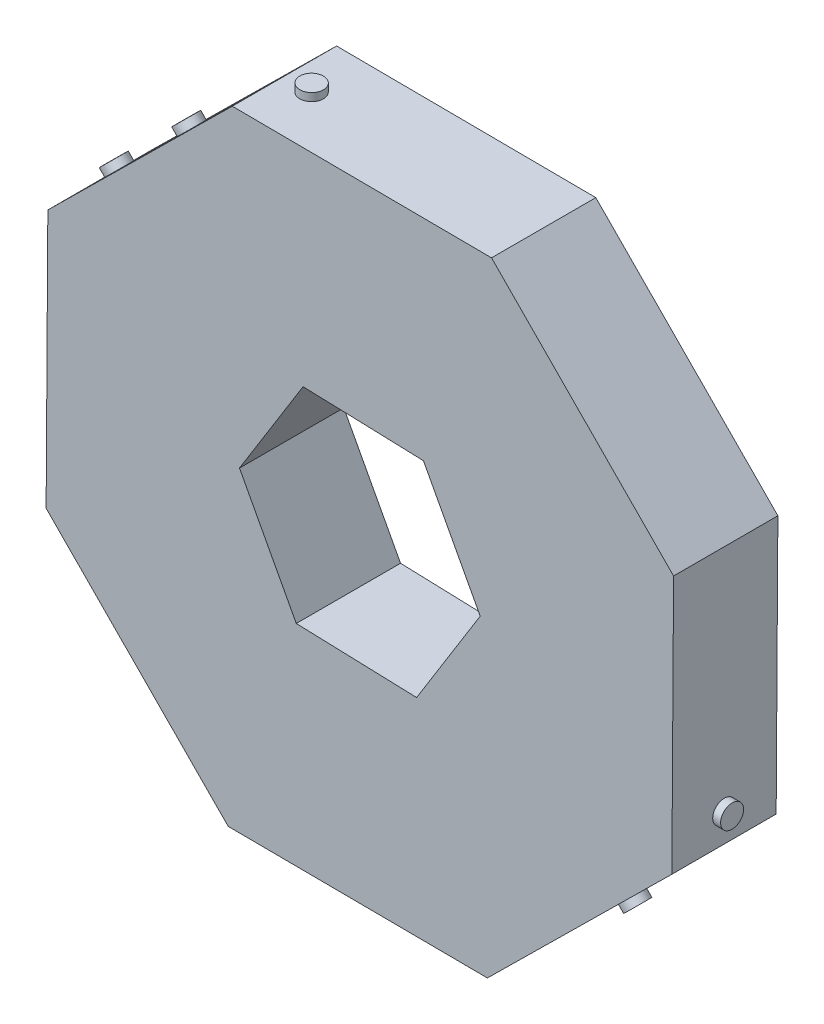
SolidWorks part; units mm, degrees
ref_plane "Front Plane" through (0, 0, 0) normal (0, 0, 1) x (1, 0, 0)
ref_plane "Top Plane" through (0, 0, 0) normal (0, 1, 0) x (1, 0, 0)
ref_plane "Right Plane" through (0, 0, 0) normal (1, 0, 0) x (0, 0, -1)
sketch "Sketch1" plane through (0, 0, 0) normal (0, 0, 1) x (1, 0, 0)
  line L1 (-7.7649, 19.1017) -> (-18.9975, 8.0163)
  line L2 (-18.9975, 8.0163) -> (-19.1017, -7.7649)
  line L3 (-19.1017, -7.7649) -> (-8.0163, -18.9975)
  line L4 (-8.0163, -18.9975) -> (7.7649, -19.1017)
  line L5 (7.7649, -19.1017) -> (18.9975, -8.0163)
  line L6 (18.9975, -8.0163) -> (19.1017, 7.7649)
  line L7 (19.1017, 7.7649) -> (8.0163, 18.9975)
  line L8 (8.0163, 18.9975) -> (-7.7649, 19.1017)
  circle A0 centre (0, 0) radius 19.05 construction
  dimension "D1" = 38.1
extrude "Boss-Extrude1" add sketch "Sketch1" along normal blind 6.35
sketch "Sketch2" plane through (0.1257, 19.0496, 0) normal (0.0066, 1, 0) x (1, -0.0066, 0)
  line L0 (-7.8908, -6.35) -> (-7.8908, 0) construction
  line L1 (7.8908, 0) -> (-7.8908, 0) construction
  circle A0 centre (-6.2398, -3.175) radius 0.72
  dimension "D1" = 1.44
  dimension "D2" = 1.651
  dimension "D3" = 3.175
extrude "Boss-Extrude2" add sketch "Sketch2" along normal blind 0.48
sketch "Sketch3" plane through (-13.3812, 13.559, 0) normal (-0.7024, 0.7118, 0) x (0.7118, 0.7024, 0)
  line L0 (-7.8908, -6.35) -> (-7.8908, 0) construction
  line L1 (7.8908, 0) -> (-7.8908, 0) construction
  circle A0 centre (-6.2398, -3.175) radius 0.72
  circle A1 centre (-0.0398, -3.175) radius 0.72
  dimension "D1" = 1.44
  dimension "D2" = 1.44
  dimension "D3" = 1.651
  dimension "D4" = 6.2
  dimension "D5" = 3.175
extrude "Boss-Extrude3" add sketch "Sketch3" along normal blind 0.48
sketch "Sketch4" plane through (-19.0496, 0.1257, 0) normal (-1, 0.0066, 0) x (0, 0, 1)
  line L0 (6.35, -7.8908) -> (0, -7.8908) construction
  line L1 (0, 7.8908) -> (0, -7.8908) construction
  circle A0 centre (3.175, -6.2398) radius 0.72
  circle A1 centre (3.175, 0.0002) radius 0.72
  circle A2 centre (3.175, 6.2402) radius 0.72
  point P10 (0, 0)
  point P11 (0, 0)
  dimension "D1" = 1.44
  dimension "D2" = 1.44
  dimension "D3" = 1.44
  dimension "D4" = 1.651
  dimension "D5" = 6.24
  dimension "D6" = 6.24
  dimension "D7" = 3.175
extrude "Boss-Extrude4" add sketch "Sketch4" along normal blind 0.48
sketch "Sketch5" plane through (-13.559, -13.3812, 0) normal (-0.7118, -0.7024, 0) x (0, 0, 1)
  line L1 (6.35, -7.8908) -> (0, -7.8908) construction
  line L2 (0, 7.8908) -> (0, -7.8908) construction
  circle A0 centre (3.175, -6.2398) radius 0.7
  circle A1 centre (3.175, 6.1602) radius 0.7
  point P6 (0, 0)
  dimension "D1" = 1.4
  dimension "D2" = 1.4
  dimension "D3" = 1.651
  dimension "D4" = 12.4
  dimension "D5" = 3.175
extrude "Boss-Extrude5" add sketch "Sketch5" along normal blind 0.48
sketch "Sketch6" plane through (-0.1257, -19.0496, 0) normal (-0.0066, -1, 0) x (-1, 0.0066, 0)
  line L0 (-7.8908, -6.35) -> (-7.8908, 0) construction
  line L1 (7.8908, 0) -> (-7.8908, 0) construction
  circle A0 centre (-0.0398, -3.175) radius 0.7
  circle A1 centre (6.1602, -3.175) radius 0.7
  dimension "D1" = 1.4
  dimension "D2" = 1.4
  dimension "D3" = 7.851
  dimension "D4" = 6.2
  dimension "D5" = 3.175
  dimension "D6" = 3.175
extrude "Boss-Extrude6" add sketch "Sketch6" along normal blind 0.48
sketch "Sketch7" plane through (13.3812, -13.559, 0) normal (0.7024, -0.7118, 0) x (-0.7118, -0.7024, 0)
  line L0 (-7.8908, -6.35) -> (-7.8908, 0) construction
  line L1 (7.8908, -6.35) -> (-7.8908, -6.35) construction
  circle A0 centre (-0.0398, -3.175) radius 0.7
  dimension "D1" = 1.4
  dimension "D2" = 7.851
  dimension "D3" = 3.175
extrude "Boss-Extrude7" add sketch "Sketch7" along normal blind 0.48
sketch "Sketch8" plane through (19.0496, -0.1257, 0) normal (1, -0.0066, 0) x (0, 0, -1)
  line L0 (-6.35, -7.8908) -> (-6.35, 7.8908) construction
  line L1 (-6.35, 7.8908) -> (0, 7.8908) construction
  circle A0 centre (-3.175, -6.1602) radius 0.7
  dimension "D1" = 1.4
  dimension "D2" = 3.175
  dimension "D3" = 14.051
extrude "Boss-Extrude8" add sketch "Sketch8" along normal blind 0.48
sketch "Sketch9" plane through (0, 0, 0) normal (0, 0, -1) x (-1, 0, 0)
  line L1 (-3.8723, 6.2264) -> (-7.3284, -0.2403)
  line L2 (-7.3284, -0.2403) -> (-3.4561, -6.4667)
  line L3 (-3.4561, -6.4667) -> (3.8723, -6.2264)
  line L4 (3.8723, -6.2264) -> (7.3284, 0.2403)
  line L5 (7.3284, 0.2403) -> (3.4561, 6.4667)
  line L6 (3.4561, 6.4667) -> (-3.8723, 6.2264)
  circle A0 centre (0, 0) radius 6.35 construction
  dimension "D1" = 12.7
extrude "Cut-Extrude1" cut sketch "Sketch9" against normal through all contours L1 L2 L3 L4 L5 L6
